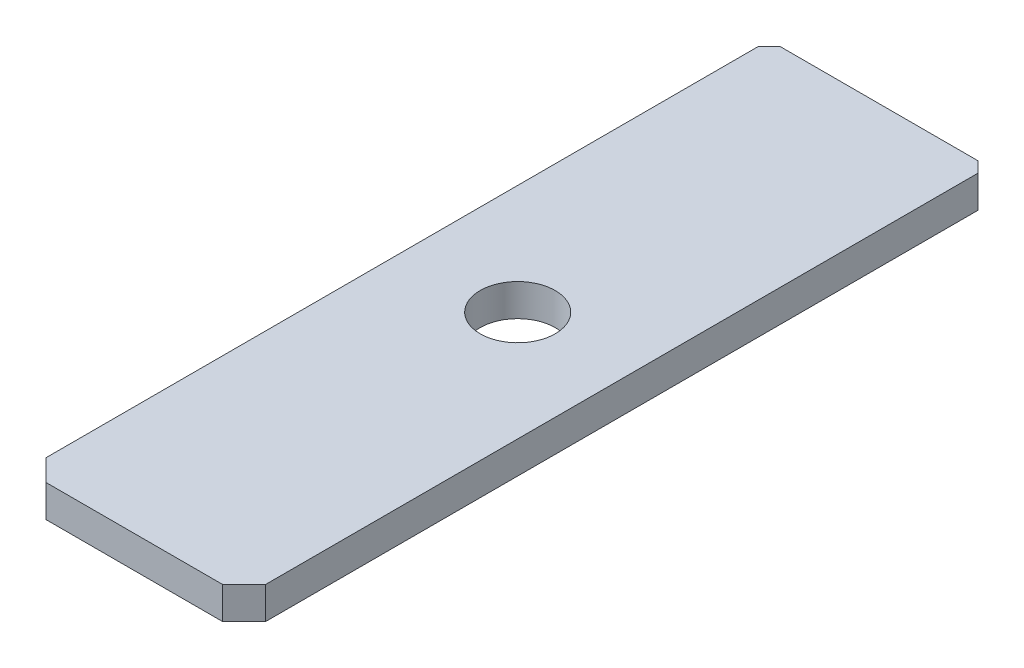
SolidWorks part; units mm, degrees
ref_plane "Front Plane" through (0, 0, 0) normal (0, 0, 1) x (1, 0, 0)
ref_plane "Top Plane" through (0, 0, 0) normal (0, 1, 0) x (1, 0, 0)
ref_plane "Right Plane" through (0, 0, 0) normal (1, 0, 0) x (0, 0, -1)
sketch "Sketch1" plane through (0, 0, 0) normal (0, 1, 0) x (1, 0, 0)
  line L1 (-5.12, 17.365) -> (5.12, 17.365)
  line L2 (-5.12, 17.365) -> (-5.12, -17.365)
  line L3 (-5.12, -17.365) -> (5.12, -17.365)
  line L4 (5.12, 17.365) -> (5.12, -17.365)
  line L5 (-5.12, 17.365) -> (5.12, -17.365) construction
  line L6 (-5.12, -17.365) -> (5.12, 17.365) construction
  point P0 (0, 0)
  dimension "D1" = 10.24
  dimension "D2" = 34.73
extrude "Boss-Extrude1" add sketch "Sketch1" along normal blind 1.5
chamfer "Chamfer1" distance 0.5 angle 45 2 edges at (-5.12, 0.75, -17.365) (5.12, 0.75, -17.365)
chamfer "Chamfer2" distance 1 angle 45 2 edges at (-5.12, 0.75, 17.365) (5.12, 0.75, 17.365)
sketch "Sketch2" plane through (0, 1.5, 0) normal (0, 1, 0) x (1, 0, 0)
  line L0 (0, -10.7116) -> (0, 3.8362) construction
  line L1 (4.62, 17.365) -> (-4.62, 17.365) construction
  circle A0 centre (0, 0.515) radius 1.75
  dimension "D1" = 3.5
  dimension "D2" = 16.85
extrude "Cut-Extrude1" cut sketch "Sketch2" against normal through all
